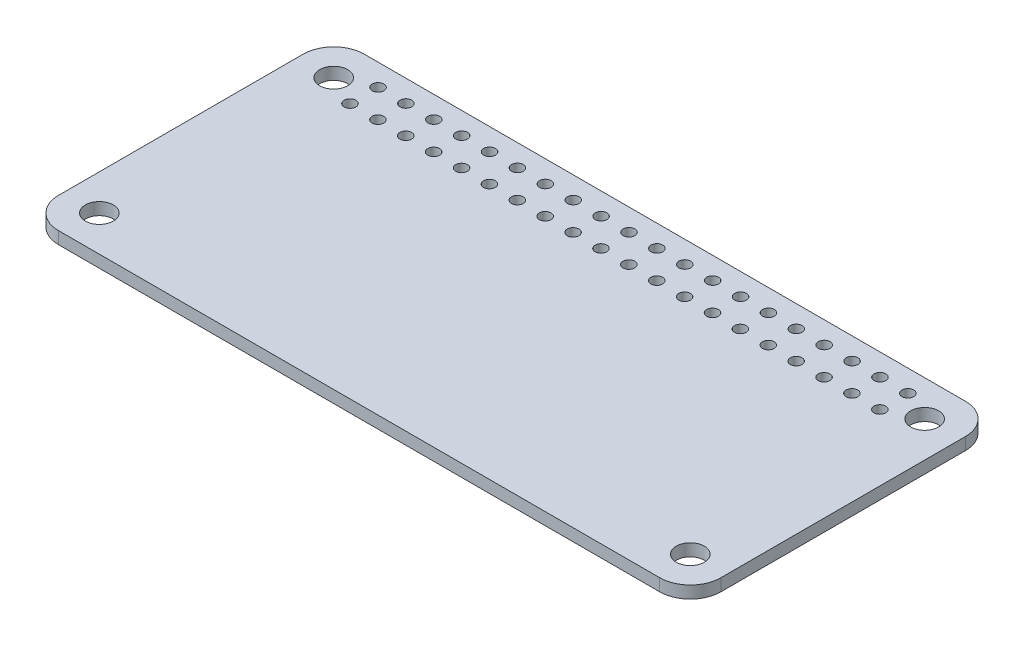
SolidWorks part; units mm, degrees
ref_plane "Front Plane" through (0, 0, 0) normal (0, 0, 1) x (1, 0, 0)
ref_plane "Top Plane" through (0, 0, 0) normal (0, 1, 0) x (1, 0, 0)
ref_plane "Right Plane" through (0, 0, 0) normal (1, 0, 0) x (0, 0, -1)
sketch "Sketch1" plane through (0, 0, 0) normal (0, 1, 0) x (1, 0, 0)
  line L1 (3, 0) -> (62, 0)
  line L2 (0, 3) -> (0, 27)
  line L3 (3, 30) -> (62, 30)
  line L4 (65, 3) -> (65, 27)
  arc A0 (62, 30) -> (65, 27) centre (62, 27) cw
  arc A1 (62, 0) -> (65, 3) centre (62, 3) ccw
  arc A2 (3, 0) -> (0, 3) centre (3, 3) cw
  arc A3 (0, 27) -> (3, 30) centre (3, 27) cw
  circle A8 centre (6.5, 27.85) radius 0.575
  circle A9 centre (9.2368, 27.85) radius 0.575
  circle A10 centre (11.9737, 27.85) radius 0.575
  circle A11 centre (14.7105, 27.85) radius 0.575
  circle A12 centre (17.4474, 27.85) radius 0.575
  circle A13 centre (20.1842, 27.85) radius 0.575
  circle A14 centre (22.9211, 27.85) radius 0.575
  circle A15 centre (25.6579, 27.85) radius 0.575
  circle A16 centre (28.3947, 27.85) radius 0.575
  circle A17 centre (31.1316, 27.85) radius 0.575
  circle A18 centre (33.8684, 27.85) radius 0.575
  circle A19 centre (36.6053, 27.85) radius 0.575
  circle A20 centre (39.3421, 27.85) radius 0.575
  circle A21 centre (42.0789, 27.85) radius 0.575
  circle A22 centre (44.8158, 27.85) radius 0.575
  circle A23 centre (47.5526, 27.85) radius 0.575
  circle A24 centre (50.2895, 27.85) radius 0.575
  circle A25 centre (53.0263, 27.85) radius 0.575
  circle A26 centre (55.7632, 27.85) radius 0.575
  circle A27 centre (58.5, 27.85) radius 0.575
  circle A28 centre (9.2368, 25.1) radius 0.575
  circle A29 centre (11.9737, 25.1) radius 0.575
  circle A30 centre (14.7105, 25.1) radius 0.575
  circle A31 centre (17.4474, 25.1) radius 0.575
  circle A32 centre (20.1842, 25.1) radius 0.575
  circle A33 centre (22.9211, 25.1) radius 0.575
  circle A34 centre (25.6579, 25.1) radius 0.575
  circle A35 centre (28.3947, 25.1) radius 0.575
  circle A36 centre (31.1316, 25.1) radius 0.575
  circle A37 centre (33.8684, 25.1) radius 0.575
  circle A38 centre (36.6053, 25.1) radius 0.575
  circle A39 centre (39.3421, 25.1) radius 0.575
  circle A40 centre (42.0789, 25.1) radius 0.575
  circle A41 centre (44.8158, 25.1) radius 0.575
  circle A42 centre (47.5526, 25.1) radius 0.575
  circle A43 centre (50.2895, 25.1) radius 0.575
  circle A44 centre (53.0263, 25.1) radius 0.575
  circle A45 centre (55.7632, 25.1) radius 0.575
  circle A46 centre (58.5, 25.1) radius 0.575
  circle A47 centre (6.5, 25.1) radius 0.575
  circle A48 centre (3.5, 26.5) radius 1.375
  circle A49 centre (61.5, 26.5) radius 1.375
  circle A50 centre (61.5, 3.5) radius 1.375
  circle A51 centre (3.5, 3.5) radius 1.375
  point P7 (65, 30)
  point P12 (0, 0)
  point P15 (0, 30)
  dimension "D3" = 3
  dimension "D4" = 3.5
  dimension "D7" = 1.15
  dimension "D8" = 2.15
  dimension "D10" = 2.75
  dimension "D1" = 65
  dimension "D2" = 30
  dimension "D9" = 3.5
  dimension "D11" = 6.5
  dimension "D12" = 6.5
  dimension "D13" = 2.75
  dimension "D5" = 20
  dimension "D6" = 2
  dimension "D14" = 2
  dimension "D15" = 2
extrude "Boss-Extrude1" add sketch "Sketch1" along normal blind 1.2
